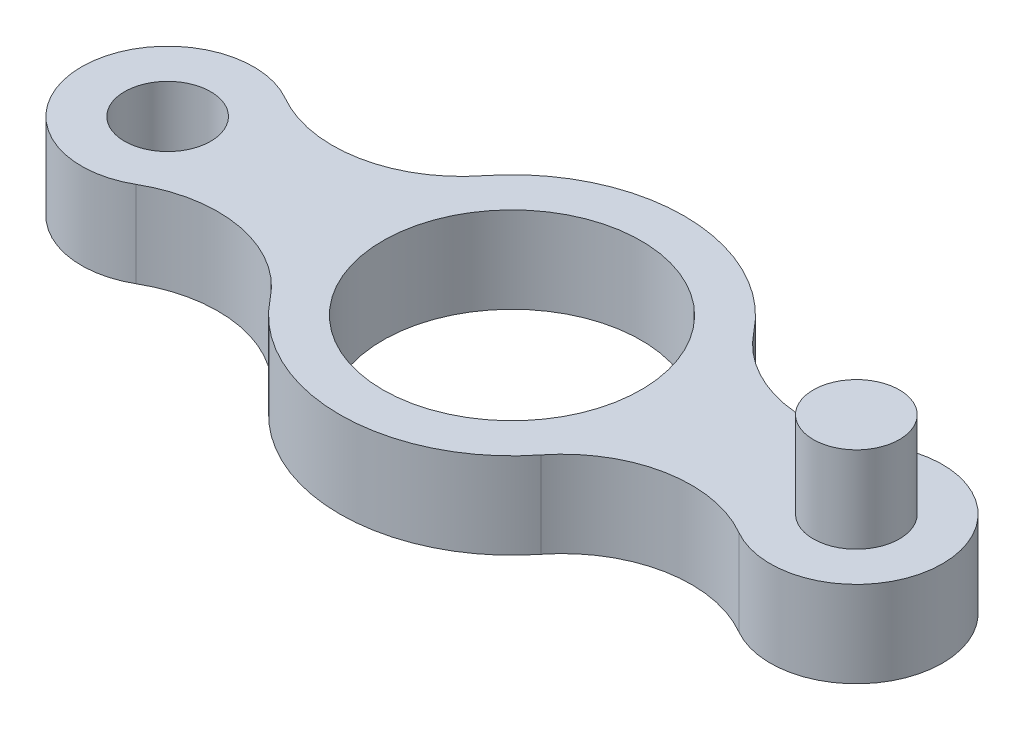
SolidWorks part; units mm, degrees
material "Thornel Mat VMA"
ref_plane "Alzado" through (0, 0, 0) normal (0, 0, 1) x (1, 0, 0)
ref_plane "Planta" through (0, 0, 0) normal (0, 1, 0) x (1, 0, 0)
ref_plane "Vista lateral" through (0, 0, 0) normal (1, 0, 0) x (0, 0, -1)
sketch "Croquis1" plane through (0, 0, 0) normal (0, 1, 0) x (1, 0, 0)
  line L0 (0, 90.3484) -> (0, 0) construction
  line L1 (117.2951, 0) -> (0, 0) construction
  line L2 (0, 0) -> (-171.1857, 0) construction
  line L3 (0, -40) -> (0, -108.4633) construction
  arc A1 (70, -17.3205) -> (70, 17.3205) centre (80, 0) ccw
  arc A2 (31.4286, 24.7436) -> (70, 17.3205) centre (55, 43.3013) ccw
  arc A3 (31.4286, 24.7436) -> (-31.4286, 24.7436) centre (0, 0) ccw
  arc A4 (-70, -17.3205) -> (-70, 17.3205) centre (-80, 0) cw
  arc A5 (-31.4286, 24.7436) -> (-70, 17.3205) centre (-55, 43.3013) cw
  arc A6 (31.4286, -24.7436) -> (70, -17.3205) centre (55, -43.3013) cw
  arc A7 (31.4286, -24.7436) -> (-31.4286, -24.7436) centre (0, 0) cw
  arc A8 (-31.4286, -24.7436) -> (-70, -17.3205) centre (-55, -43.3013) ccw
  dimension "D2" = 40
  dimension "D4" = 60
  dimension "DISTANCIA ENTRE CÍRCULO Y CENTRO" = 80
extrude "Saliente-Extruir1" add sketch "Croquis1" along normal blind 20
sketch "Croquis2" plane through (0, 20, 0) normal (0, 1, 0) x (1, 0, 0)
  circle A0 centre (0, 0) radius 30
  dimension "PERFORACIÓN CÍRCULO CENTRAL" = 60
extrude "Cortar-Extruir1" cut sketch "Croquis2" against normal through all
sketch "Croquis3" plane through (0, 20, 0) normal (0, 1, 0) x (1, 0, 0)
  circle A0 centre (-80, 0) radius 10
  dimension "PERFORACIÓN CÍRCULO PEQUEÑO" = 20
extrude "Cortar-Extruir2" cut sketch "Croquis3" against normal through all
sketch "Croquis4" plane through (0, 20, 0) normal (0, 1, 0) x (1, 0, 0)
  circle A0 centre (80, 0) radius 10
  dimension "VASTAGO CÍRCULO PEQUEÑO" = 20
extrude "Saliente-Extruir2" add sketch "Croquis4" along normal blind 20
